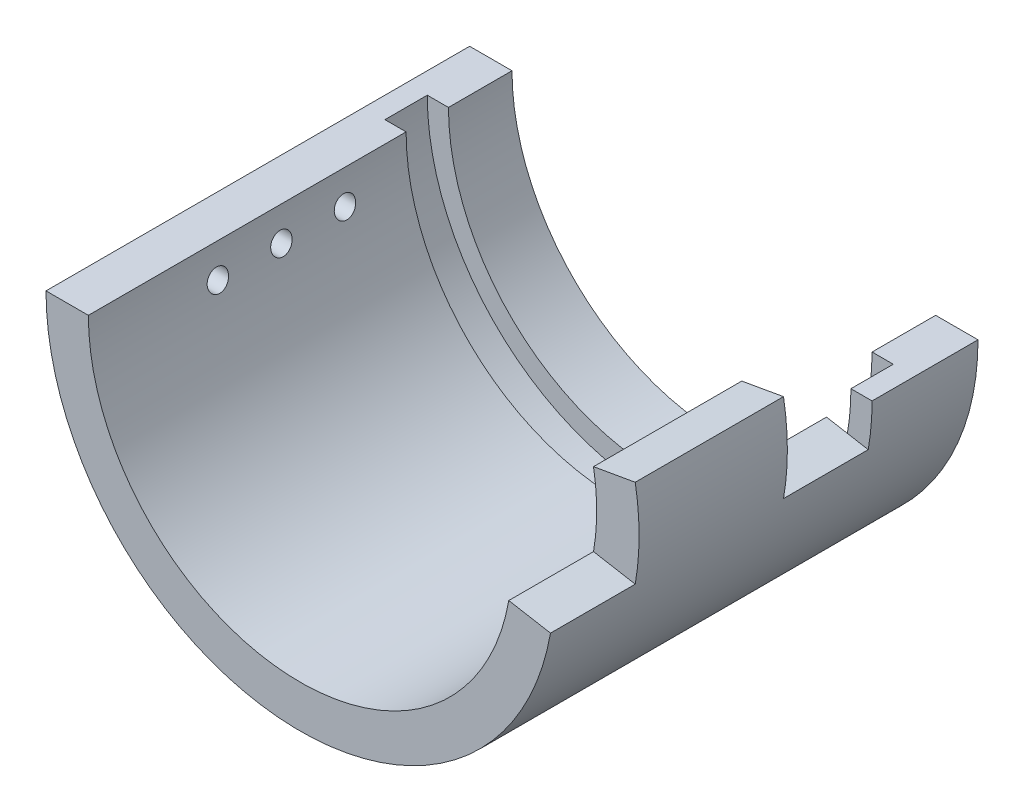
SolidWorks part; units mm, degrees
ref_plane "Front Plane" through (0, 0, 0) normal (0, 0, 1) x (1, 0, 0)
ref_plane "Top Plane" through (0, 0, 0) normal (0, 1, 0) x (1, 0, 0)
ref_plane "Right Plane" through (0, 0, 0) normal (1, 0, 0) x (0, 0, -1)
sketch "Sketch1" plane through (0, 0, 0) normal (0, 1, 0) x (1, 0, 0)
  line L0 (0, 69.1176) -> (0, -71.4706) construction
  line L1 (-60, 19.1176) -> (-60, -80.8824)
  line L2 (-60, 19.1176) -> (-50, 19.1176)
  line L3 (-50, 19.1176) -> (-50, 4.1176)
  line L4 (-50, 4.1176) -> (-55, 4.1176)
  line L5 (-55, 4.1176) -> (-55, -5.8824)
  line L6 (-55, -5.8824) -> (-50, -5.8824)
  line L7 (-50, -5.8824) -> (-50, -80.8824)
  line L8 (-50, -80.8824) -> (-60, -80.8824)
  dimension "D1" = 15
  dimension "D2" = 10
  dimension "D3" = 5
  dimension "D4" = 10
  dimension "D5" = 10
  dimension "D6" = 100
  dimension "D7" = 50
revolve "Revolve1" add sketch "Sketch1" angle 180 about L0
ref_plane "Plane1" through (60, 0, 0) normal (1, 0, 0) x (0, 0, -1)
sketch "Sketch2" plane through (0, 0, 0) normal (0, 1, 0) x (1, 0, 0)
  line L0 (50, -5.8824) -> (60, -5.8824)
  line L1 (60, 19.1176) -> (60, -80.8824) construction
  line L2 (60, -5.8824) -> (60, -80.8824)
  line L3 (60, -80.8824) -> (50, -80.8824)
  line L4 (50, -80.8824) -> (50, -5.8824)
  line L5 (60, -25.8824) -> (50, -25.8824)
  line L6 (60, -60.8824) -> (50, -60.8824)
  line L7 (0, 76.2744) -> (0, -88.6556) construction
  line L8 (0, -55) -> (0, 55) construction
  line L10 (60, -5.8824) -> (50, -5.8824)
  line L11 (60, -5.8824) -> (60, -25.8824)
  line L12 (60, -25.8824) -> (50, -25.8824)
  line L13 (50, -5.8824) -> (50, -25.8824)
  dimension "D1" = 20
  dimension "D2" = 20
revolve "Revolve2" add sketch "Sketch2" angle 10 about L7
sketch "Sketch3" plane through (0, 0, 0) normal (0, 1, 0) x (1, 0, 0)
  line L0 (50, -80.8824) -> (50, -60.8824)
  line L1 (50, -5.8824) -> (60, -5.8824)
  line L2 (60, 19.1176) -> (60, -25.8824) construction
  line L3 (60, -5.8824) -> (60, -25.8824)
  line L4 (60, -25.8824) -> (50, -25.8824)
  line L5 (50, -25.8824) -> (50, -5.8824)
  line L6 (60, -60.8824) -> (60, -80.8824)
  line L7 (50, -80.8824) -> (50, -60.8824) construction
  line L8 (60, -80.8824) -> (50, -80.8824)
  line L9 (0, 76.8347) -> (0, -88.1291) construction
  line L10 (0, -38.7304) -> (0, 38.7304) construction
  line L11 (59.0885, -60.8824) -> (49.2404, -60.8824) construction
  line L12 (50, -60.8824) -> (60, -60.8824)
revolve "Cut-Revolve1" cut sketch "Sketch3" angle 10 about L9
ref_plane "Plane2" through (-80, 0, 0) normal (1, 0, 0) x (0, 0, -1)
sketch "Sketch5" plane through (-80, 0, 0) normal (1, 0, 0) x (0, 0, -1)
  line L0 (19.1176, 0) -> (-80.8824, 0) construction
  line L1 (-80.8824, 0) -> (-80.8824, -60) construction
  circle A0 centre (-35.8824, -7.5) radius 2.5
  circle A1 centre (-50.8824, -7.5) radius 2.5
  circle A2 centre (-20.8824, -7.5) radius 2.5
  dimension "D1" = 5
  dimension "D2" = 5
  dimension "D3" = 5
  dimension "D4" = 15
  dimension "D5" = 15
  dimension "D6" = 7.5
  dimension "D7" = 30
extrude "Cut-Extrude2" cut sketch "Sketch5" along normal up to next
